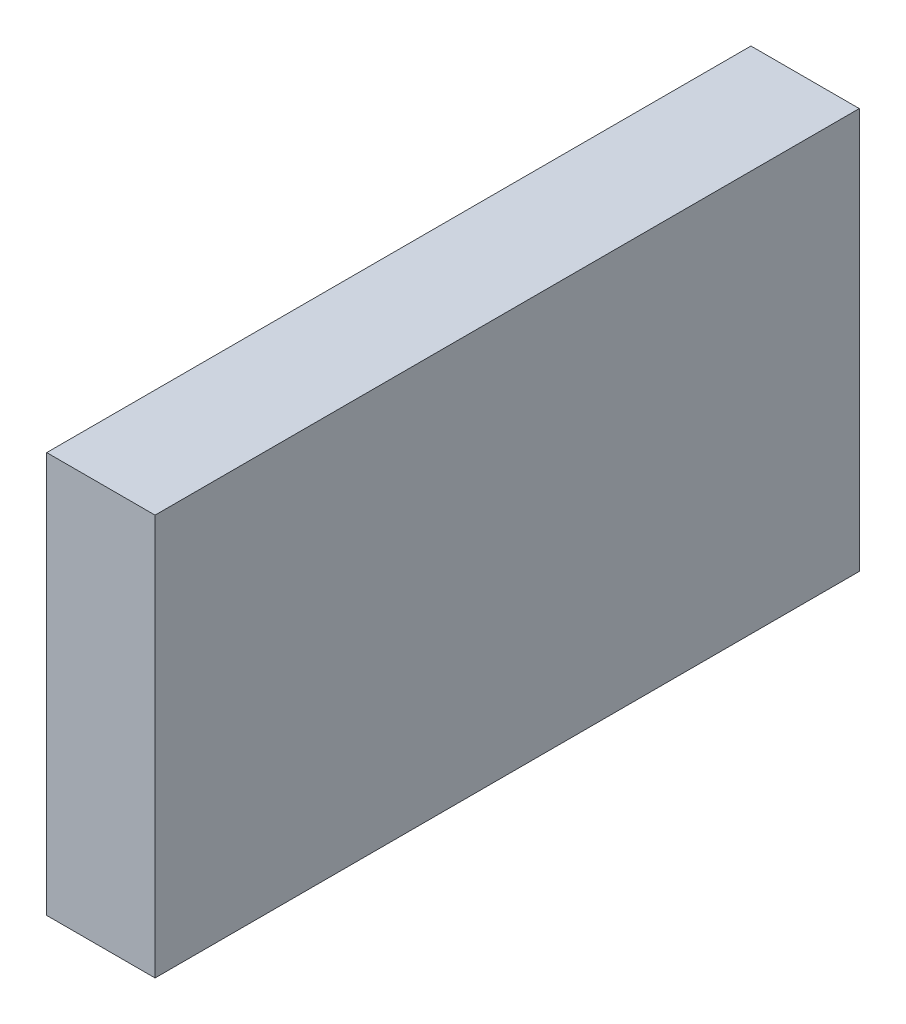
SolidWorks part; units mm, degrees
ref_plane "Front Plane" through (0, 0, 0) normal (0, 0, 1) x (1, 0, 0)
ref_plane "Top Plane" through (0, 0, 0) normal (0, 1, 0) x (1, 0, 0)
ref_plane "Right Plane" through (0, 0, 0) normal (1, 0, 0) x (0, 0, -1)
sketch "Sketch1" plane through (0, 0, 0) normal (0, 0, 1) x (1, 0, 0)
  line L1 (0, 0) -> (5.08, 0)
  line L2 (0, 0) -> (0, 18.796)
  line L3 (0, 18.796) -> (5.08, 18.796)
  line L4 (5.08, 0) -> (5.08, 18.796)
  dimension "D1" = 5.08
  dimension "D2" = 18.796
extrude "Boss-Extrude1" add sketch "Sketch1" along normal blind 33.02
